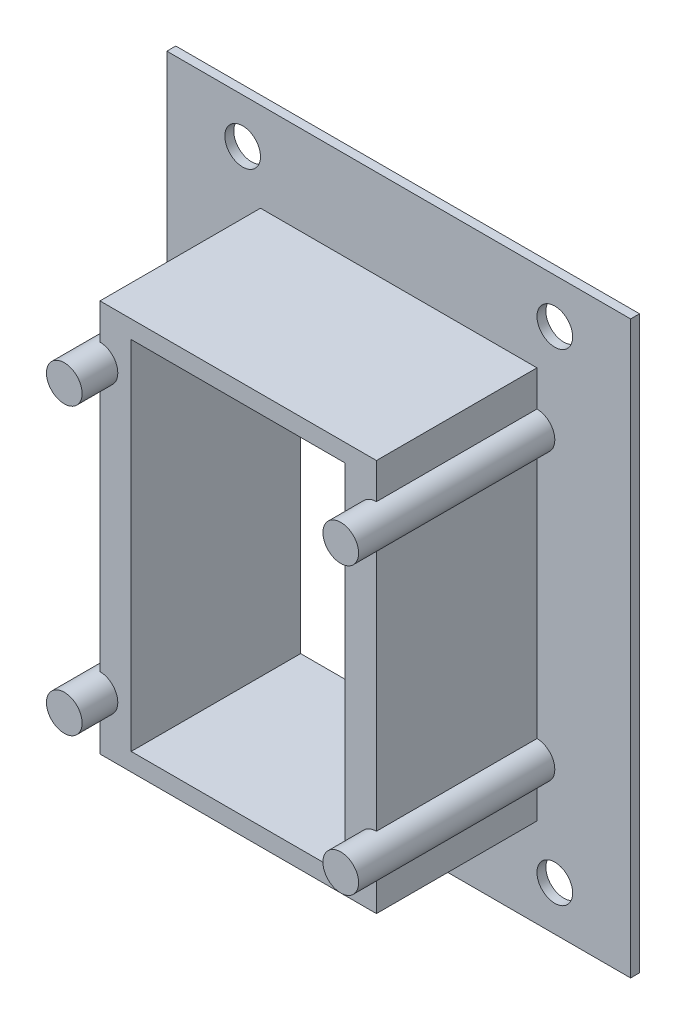
SolidWorks part; units mm, degrees
ref_plane "Front Plane" through (0, 0, 0) normal (0, 0, 1) x (1, 0, 0)
ref_plane "Top Plane" through (0, 0, 0) normal (0, 1, 0) x (1, 0, 0)
ref_plane "Right Plane" through (0, 0, 0) normal (1, 0, 0) x (0, 0, -1)
sketch "Sketch1" plane through (0, 0, 0) normal (0, 0, 1) x (1, 0, 0)
  line L1 (-41.275, -50.8) -> (41.275, -50.8)
  line L2 (-41.275, -50.8) -> (-41.275, 50.8)
  line L3 (-41.275, 50.8) -> (41.275, 50.8)
  line L4 (41.275, -50.8) -> (41.275, 50.8)
  line L5 (-41.275, -50.8) -> (41.275, 50.8) construction
  line L6 (-41.275, 50.8) -> (41.275, -50.8) construction
  point P0 (0, 0)
  dimension "D1" = 101.6
  dimension "D2" = 82.55
extrude "Boss-Extrude1" add sketch "Sketch1" along normal blind 1.5875
sketch "Sketch2" plane through (0, 0, 1.5875) normal (0, 0, 1) x (1, 0, 0)
  line L1 (-24.6062, -34.925) -> (24.6062, -34.925)
  line L2 (-24.6062, -34.925) -> (-24.6062, 34.925)
  line L3 (-24.6062, 34.925) -> (24.6062, 34.925)
  line L4 (24.6062, -34.925) -> (24.6062, 34.925)
  line L5 (-24.6062, -34.925) -> (24.6062, 34.925) construction
  line L6 (-24.6062, 34.925) -> (24.6062, -34.925) construction
  point P0 (0, 0)
  dimension "D1" = 49.2125
  dimension "D2" = 69.85
extrude "Boss-Extrude2" add sketch "Sketch2" along normal blind 28.575
sketch "Sketch3" plane through (0, 0, 1.5875) normal (0, 0, 1) x (1, 0, 0)
  line L0 (-24.6062, 34.925) -> (-24.6062, -34.925) construction
  line L1 (24.6062, -34.925) -> (24.6062, 34.925) construction
  line L2 (-24.6062, 34.925) -> (-24.6062, -34.925) construction
  line L3 (-24.6062, 0) -> (24.6062, 0) construction
  circle A0 centre (-24.6062, 25.4) radius 3.175
  circle A1 centre (24.6062, 25.4) radius 3.175
  circle A2 centre (-24.6062, -25.4) radius 3.175
  circle A3 centre (24.6062, -25.4) radius 3.175
  point P16 (0, 0)
  point P17 (0, 0)
  point P18 (0, 0)
  point P19 (0, 0)
  dimension "D2" = 6.35
  dimension "D1" = 50.8
extrude "Boss-Extrude3" add sketch "Sketch3" along normal blind 34.925
hole_wizard "1/4 (0.25) Diameter Hole1" positions "Sketch4" profile "Sketch5" hole size "1/4" standard "ANSI Inch" end condition through all
sketch "Sketch4" plane through (0, 0, 1.5875) normal (0, 0, 1) x (1, 0, 0)
  line L0 (-27.7812, 42.8625) -> (27.7813, -42.8625) construction
  line L3 (27.7813, 42.8625) -> (-27.7812, -42.8625) construction
  point P0 (-27.7812, 42.8625)
  point P2 (27.7813, 42.8625)
  point P4 (-27.7812, -42.8625)
  point P6 (27.7813, -42.8625)
  dimension "D1" = 55.5625
  dimension "D2" = 85.725
sketch "Sketch5" plane through (-27.7812, 42.8625, 1.5875) normal (1, 0, 0) x (0, -1, 0)
  line L0 (0, 0) -> (0, 1.5875)
  line L1 (0, 1.5875) -> (3.175, 1.5875)
  line L2 (3.175, 1.5875) -> (3.175, 0)
  line L5 (3.175, 0) -> (0, 0)
  line L11 (0, -6.35) -> (0, 107.95) construction
  dimension "Thru Hole Dia." = 6.35
  dimension "Thru Hole Depth" = 1.5875
sketch "Sketch6" plane through (0, 0, 30.1625) normal (0, 0, 1) x (1, 0, 0)
  line L1 (19.05, -31.75) -> (-19.05, -31.75)
  line L2 (19.05, -31.75) -> (19.05, 31.75)
  line L3 (19.05, 31.75) -> (-19.05, 31.75)
  line L4 (-19.05, -31.75) -> (-19.05, 31.75)
  line L5 (19.05, -31.75) -> (-19.05, 31.75) construction
  line L6 (19.05, 31.75) -> (-19.05, -31.75) construction
  point P0 (0, 0)
  dimension "D1" = 38.1
  dimension "D2" = 63.5
extrude "Cut-Extrude1" cut sketch "Sketch6" against normal through all
